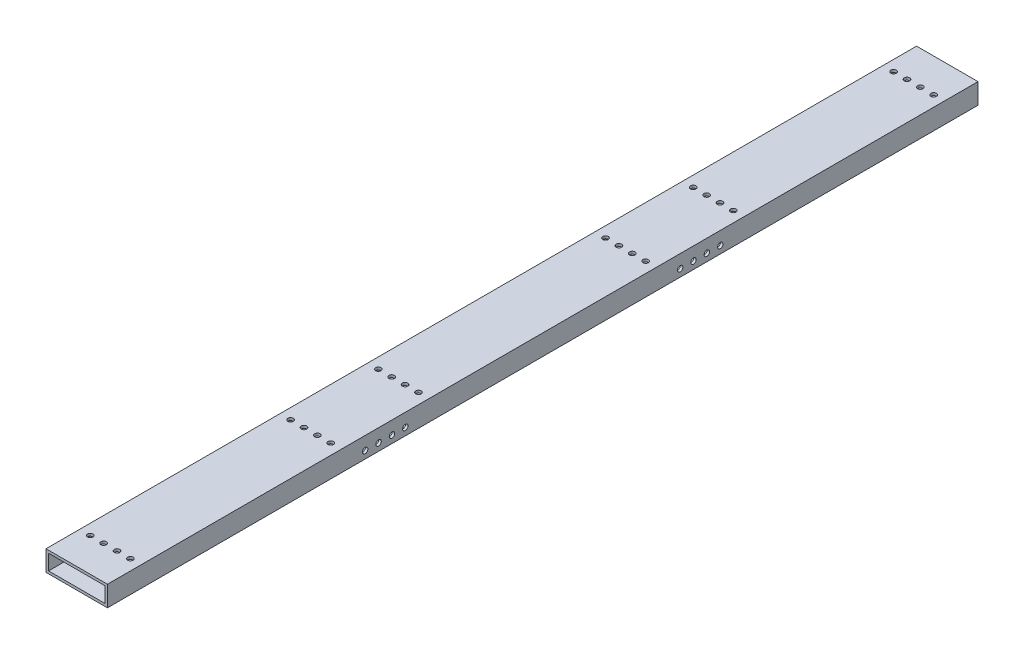
SolidWorks part; units mm, degrees
material "6061-T6 (SS)"
ref_plane "Front Plane" through (0, 0, 0) normal (0, 0, 1) x (1, 0, 0)
ref_plane "Top Plane" through (0, 0, 0) normal (0, 1, 0) x (1, 0, 0)
ref_plane "Right Plane" through (0, 0, 0) normal (1, 0, 0) x (0, 0, -1)
sketch "Sketch1" plane through (0, 0, 0) normal (0, 0, 1) x (1, 0, 0)
  line L0 (3.175, 22.225) -> (73.025, 22.225)
  line L1 (0, 0) -> (76.2, 0)
  line L2 (0, 0) -> (0, 25.4)
  line L3 (0, 25.4) -> (76.2, 25.4)
  line L4 (76.2, 0) -> (76.2, 25.4)
  line L5 (73.025, 3.175) -> (73.025, 22.225)
  line L6 (3.175, 3.175) -> (73.025, 3.175)
  line L7 (3.175, 3.175) -> (3.175, 22.225)
  dimension "D1" = 76.2
  dimension "D2" = 25.4
  dimension "D3" = 3.175
extrude "Boss-Extrude1" add sketch "Sketch1" along normal blind 1079.5
sketch "Sketch2" plane through (0, 0, 0) normal (0, -1, 0) x (1, 0, 0)
  line L0 (76.2, 1079.5) -> (76.2, 0) construction
  line L1 (0, 50.8) -> (0, 25.4) construction
  line L2 (0, 0) -> (76.2, 0) construction
  circle A1 centre (13.2131, 41.6687) radius 3.3782
  circle A2 centre (29.8044, 41.6687) radius 3.3782
  circle A4 centre (46.3956, 41.6687) radius 3.3782
  circle A6 centre (62.9869, 41.6687) radius 3.3782
  dimension "D1" = 6.7564
  dimension "D2" = 6.7564
  dimension "D3" = 6.7564
  dimension "D4" = 6.7564
  dimension "D5" = 13.2131
  dimension "D6" = 13.2131
  dimension "D7" = 16.5913
  dimension "D8" = 16.5913
  dimension "D9" = 16.5913
  dimension "D10" = 41.6687
  dimension "D11" = 41.6687
  dimension "D12" = 41.6687
extrude "Cut-Extrude1" cut sketch "Sketch2" against normal through all
ref_plane "Plane1" through (0, 0, 539.75) normal (0, 0, -1) x (-1, 0, 0)
mirror "Mirror1" about plane through (0, 0, 539.75) normal (0, 0, -1) of "Cut-Extrude1"
sketch "Sketch3" plane through (0, 25.4, 0) normal (0, 1, 0) x (1, 0, 0)
  circle A0 centre (13.2131, -789.3812) radius 3.3782
  circle A1 centre (29.8044, -789.3812) radius 3.3782
  circle A2 centre (46.3956, -789.3812) radius 3.3782
  circle A3 centre (62.9869, -789.3812) radius 3.3782
  circle A4 centre (29.8044, -680.6438) radius 3.3782
  circle A5 centre (46.3956, -680.6438) radius 3.3782
  circle A6 centre (62.9869, -680.6438) radius 3.3782
  circle A7 centre (13.2131, -290.1188) radius 3.3782
  circle A8 centre (29.8044, -290.1188) radius 3.3782
  circle A9 centre (46.3956, -290.1188) radius 3.3782
  circle A10 centre (62.9869, -290.1188) radius 3.3782
  circle A11 centre (13.2131, -398.8562) radius 3.3782
  circle A12 centre (29.8044, -398.8562) radius 3.3782
  circle A13 centre (46.3956, -398.8562) radius 3.3782
  circle A14 centre (62.9869, -398.8562) radius 3.3782
  circle A16 centre (13.2131, -680.6438) radius 3.3782
  dimension "D1" = 6.7564
  dimension "D2" = 6.7564
  dimension "D3" = 6.7564
  dimension "D4" = 6.7564
  dimension "D5" = 6.7564
  dimension "D6" = 6.7564
  dimension "D7" = 6.7564
  dimension "D8" = 6.7564
  dimension "D9" = 6.7564
  dimension "D10" = 6.7564
  dimension "D11" = 6.7564
  dimension "D12" = 6.7564
  dimension "D13" = 6.7564
  dimension "D14" = 6.7564
  dimension "D15" = 6.7564
  dimension "D16" = 6.7564
extrude "Cut-Extrude2" cut sketch "Sketch3" against normal through all
sketch "Sketch4" plane through (0, 0, 0) normal (-1, 0, 0) x (0, 0, 1)
  circle A0 centre (710.1256, 9.1313) radius 3.3782
  circle A1 centre (759.8994, 9.1313) radius 3.3782
  circle A2 centre (743.3081, 9.1313) radius 3.3782
  circle A3 centre (726.7169, 9.1313) radius 3.3782
  dimension "D1" = 6.7564
  dimension "D2" = 6.7564
  dimension "D3" = 6.7564
  dimension "D4" = 6.7564
extrude "Cut-Extrude3" cut sketch "Sketch4" against normal through all
mirror "Mirror2" about plane through (0, 0, 539.75) normal (0, 0, -1) of "Cut-Extrude3"
